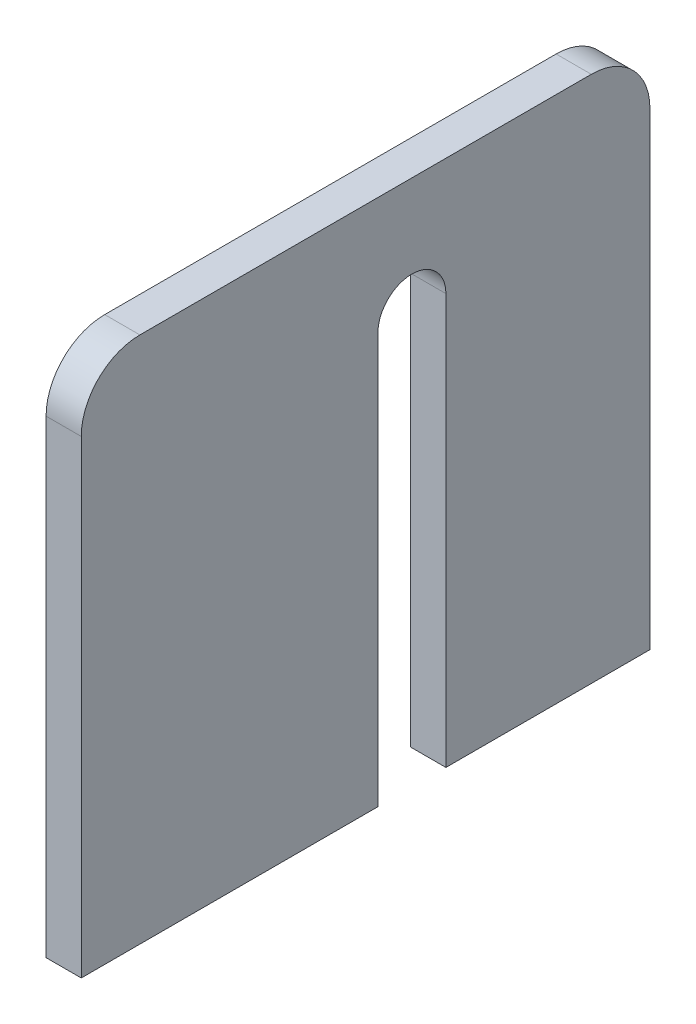
SolidWorks part; units mm, degrees
ref_plane "Front Plane" through (0, 0, 0) normal (0, 0, 1) x (1, 0, 0)
ref_plane "Top Plane" through (0, 0, 0) normal (0, 1, 0) x (1, 0, 0)
ref_plane "Right Plane" through (0, 0, 0) normal (1, 0, 0) x (0, 0, -1)
sketch "Sketch1" plane through (0, 0, 0) normal (1, 0, 0) x (0, 0, -1)
  line L1 (0, 0) -> (48.5, 0)
  line L2 (0, 0) -> (0, 45)
  line L3 (0, 45) -> (48.5, 45)
  line L4 (48.5, 0) -> (48.5, 45)
  dimension "D1" = 45
  dimension "D2" = 48.5
extrude "Boss-Extrude1" add sketch "Sketch1" along normal blind 3
sketch "Sketch2" plane through (3, 0, 0) normal (1, 0, 0) x (0, 0, -1)
  line L0 (0, 0) -> (48.5, 0) construction
  line L1 (25.3, 35) -> (25.3, 0)
  line L2 (0, 45) -> (0, 0) construction
  line L3 (25.3, 0) -> (31.1, 0)
  line L4 (31.1, 0) -> (31.1, 35)
  arc A0 (31.1, 35) -> (25.3, 35) centre (28.2, 35) ccw
  dimension "D1" = 5.8
  dimension "D2" = 35
  dimension "D3" = 28.2
extrude "Cut-Extrude1" cut sketch "Sketch2" against normal through all
fillet "Fillet1" radius 5 2 edges at (1.5, 45, -48.5) (1.5, 45, 0)
